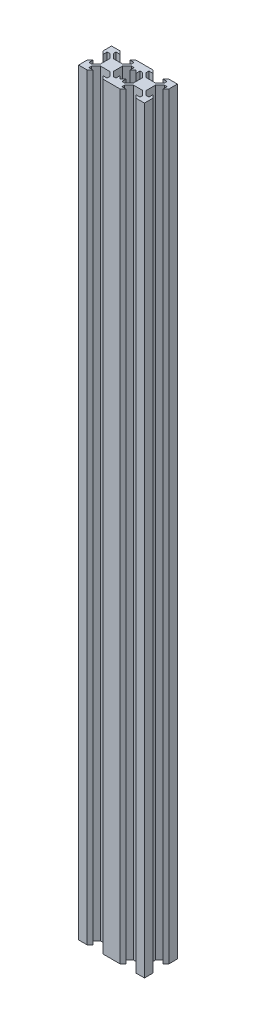
SolidWorks part; units mm, degrees
ref_plane "Front Plane" through (0, 0, 0) normal (0, 0, 1) x (1, 0, 0)
ref_plane "Top Plane" through (0, 0, 0) normal (0, 1, 0) x (1, 0, 0)
ref_plane "Right Plane" through (0, 0, 0) normal (1, 0, 0) x (0, 0, -1)
sketch "Sketch1" plane through (0, 0, 0) normal (0, 1, 0) x (1, 0, 0)
  line L0 (0, 93.8825) -> (0, -83.9719) construction
  line L1 (2.84, -3.9007) -> (-2.84, -3.9007)
  line L2 (3.9007, -2.84) -> (3.9007, 2.84)
  line L3 (2.84, 3.9007) -> (-2.84, 3.9007)
  line L4 (-3.9007, -2.84) -> (-3.9007, 2.84)
  line L7 (-194.997, 0) -> (154.5512, 0) construction
  line L8 (-2.84, -3.9007) -> (-5.4993, -6.56)
  line L9 (-5.4993, -6.56) -> (-5.4993, -8.2)
  line L10 (-5.4993, -8.2) -> (-3.1, -8.2)
  line L11 (-3.1, -8.2) -> (-4.9, -10)
  line L12 (-4.9, -10) -> (-10, -10)
  line L13 (-3.9007, -2.84) -> (-6.56, -5.4993)
  line L14 (-6.56, -5.4993) -> (-8.2, -5.4993)
  line L15 (-8.2, -5.4993) -> (-8.2, -3.1)
  line L16 (-8.2, -3.1) -> (-10, -4.9)
  line L17 (-10, -4.9) -> (-10, -10)
  line L18 (10, -4.9) -> (10, -10)
  line L19 (8.2, -3.1) -> (10, -4.9)
  line L20 (8.2, -5.4993) -> (8.2, -3.1)
  line L21 (6.56, -5.4993) -> (8.2, -5.4993)
  line L22 (3.9007, -2.84) -> (6.56, -5.4993)
  line L23 (4.9, -10) -> (10, -10)
  line L24 (3.1, -8.2) -> (4.9, -10)
  line L25 (5.4993, -8.2) -> (3.1, -8.2)
  line L26 (5.4993, -6.56) -> (5.4993, -8.2)
  line L27 (2.84, -3.9007) -> (5.4993, -6.56)
  line L28 (2.84, 3.9007) -> (5.4993, 6.56)
  line L29 (5.4993, 6.56) -> (5.4993, 8.2)
  line L30 (5.4993, 8.2) -> (3.1, 8.2)
  line L31 (3.1, 8.2) -> (4.9, 10)
  line L32 (4.9, 10) -> (10, 10)
  line L33 (3.9007, 2.84) -> (6.56, 5.4993)
  line L34 (6.56, 5.4993) -> (8.2, 5.4993)
  line L35 (8.2, 5.4993) -> (8.2, 3.1)
  line L36 (8.2, 3.1) -> (10, 4.9)
  line L37 (10, 4.9) -> (10, 10)
  line L38 (-10, 4.9) -> (-10, 10)
  line L39 (-8.2, 3.1) -> (-10, 4.9)
  line L40 (-8.2, 5.4993) -> (-8.2, 3.1)
  line L41 (-6.56, 5.4993) -> (-8.2, 5.4993)
  line L42 (-3.9007, 2.84) -> (-6.56, 5.4993)
  line L43 (-4.9, 10) -> (-10, 10)
  line L44 (-3.1, 8.2) -> (-4.9, 10)
  line L45 (-5.4993, 8.2) -> (-3.1, 8.2)
  line L46 (-5.4993, 6.56) -> (-5.4993, 8.2)
  line L47 (-2.84, 3.9007) -> (-5.4993, 6.56)
  point P0 (0, 0)
  point P4 (4.1697, 5.2303)
  dimension "D1" = 90
  dimension "D2" = 20
  dimension "D3" = 1.64
  dimension "D4" = 1.5
  dimension "D5" = 6.2
  dimension "D6" = 5.68
  dimension "D7" = 1.8
extrude "Boss-Extrude1" add sketch "Sketch1" along normal blind 460
pattern_linear "LPattern1" count 2 spacing 20 along (1, 0, 0) of "Boss-Extrude1"
